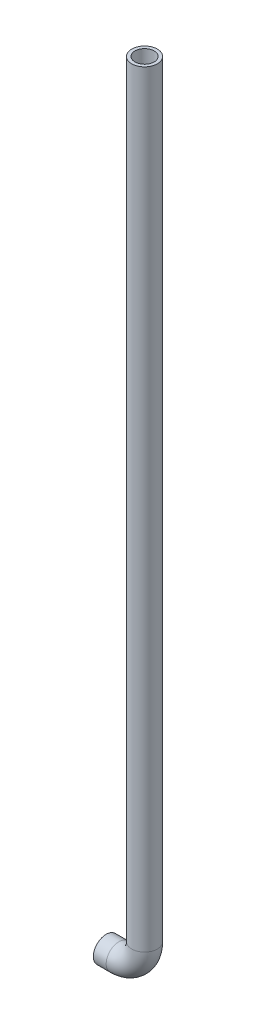
SolidWorks part; units mm, degrees
material "6061-T6"
ref_plane "Front Plane" through (0, 0, 0) normal (0, 0, 1) x (1, 0, 0)
ref_plane "Top Plane" through (0, 0, 0) normal (0, 1, 0) x (1, 0, 0)
ref_plane "Right Plane" through (0, 0, 0) normal (1, 0, 0) x (0, 0, -1)
sketch "Sketch1" plane through (0, 0, 0) normal (0, 0, 1) x (1, 0, 0)
  line L0 (38.1, 786.13) -> (38.1, 25.4)
  line L1 (12.7, 0) -> (0, 0)
  arc A0 (38.1, 25.4) -> (12.7, 0) centre (12.7, 25.4) cw
  dimension "D3" = 25.4
  dimension "D1" = 786.13
  dimension "D2" = 12.7
sweep "Sweep1" add path "Sketch1" circular profile diameter 25.4 parameters "D3"=25.4
shell "Shell2" thickness 3.175
